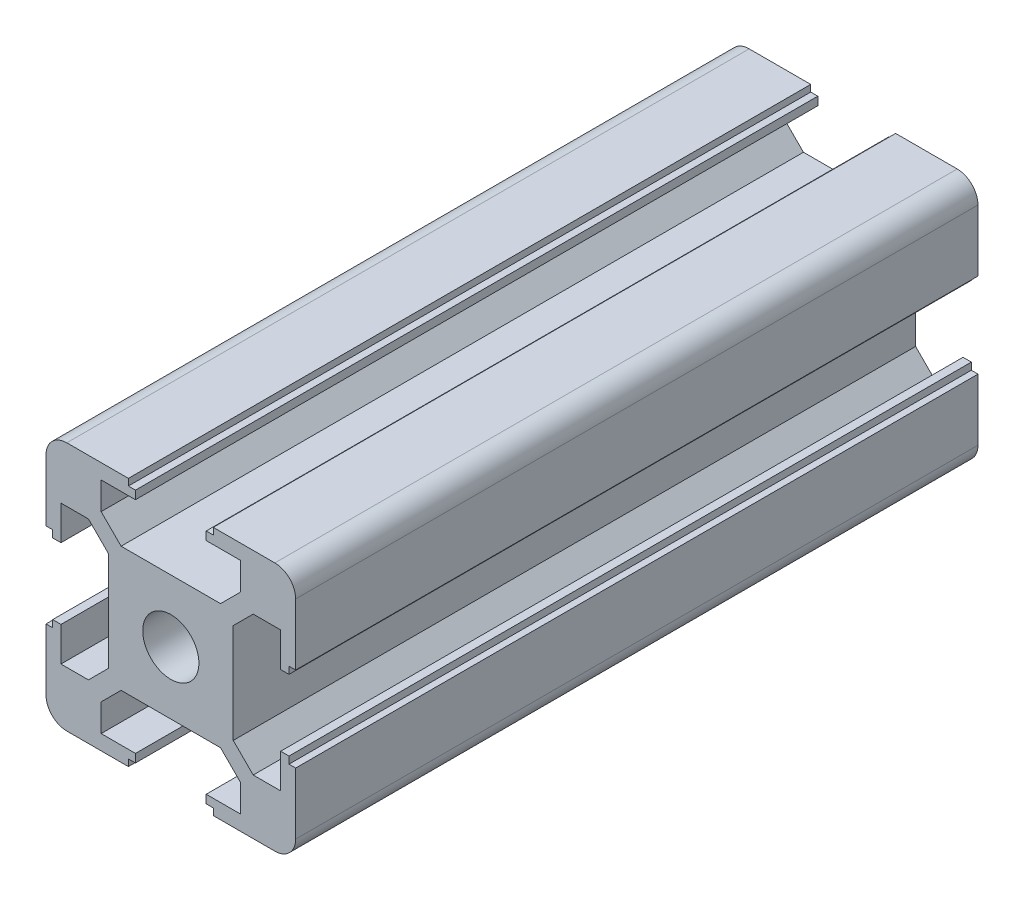
SolidWorks part; units mm, degrees
ref_plane "Front Plane" through (0, 0, 0) normal (0, 0, 1) x (1, 0, 0)
ref_plane "Top Plane" through (0, 0, 0) normal (0, 1, 0) x (1, 0, 0)
ref_plane "Right Plane" through (0, 0, 0) normal (1, 0, 0) x (0, 0, -1)
sketch "Sketch1" plane through (0, 0, 0) normal (0, 0, 1) x (1, 0, 0)
  line L1 (-15, -15) -> (15, -15)
  line L2 (-15, -15) -> (-15, 15)
  line L3 (-15, 15) -> (15, 15)
  line L4 (15, -15) -> (15, 15)
  line L5 (-15, -15) -> (15, 15) construction
  line L6 (-15, 15) -> (15, -15) construction
  point P0 (0, 0)
  dimension "D1" = 30
  dimension "D2" = 30
extrude "Boss-Extrude1" add sketch "Sketch1" along normal mid plane 82
sketch "Sketch2" plane through (0, 0, 41) normal (0, 0, 1) x (1, 0, 0)
  circle A0 centre (0, 0) radius 3.375
  dimension "D1" = 6.75
extrude "Cut-Extrude1" cut sketch "Sketch2" against normal through all
cosmetic thread "Cosmetic Thread1" parameters "D1"=12, "D2"=8
cosmetic thread "Cosmetic Thread2" parameters "D1"=12, "D2"=8
fillet "Fillet1" radius 2.5 4 edges at (15, -15, 0) (-15, -15, 0) (15, 15, 0) (-15, 15, 0)
sketch "Sketch3" plane through (0, 0, 41) normal (0, 0, 1) x (1, 0, 0)
  line L0 (0, -1000) -> (0, 49000) construction
  line L1 (0, 15) -> (-5.1, 15)
  line L2 (12.5, 15) -> (-12.5, 15) construction
  line L3 (-5.1, 15) -> (-5.1, 14.2)
  line L4 (-5.1, 14.2) -> (-4.25, 14.2)
  line L5 (-4.25, 14.2) -> (-4.25, 13.2)
  line L6 (-4.25, 13.2) -> (-8.375, 13.2)
  line L7 (-8.375, 13.2) -> (-8.375, 9.9)
  line L8 (-8.375, 9.9) -> (-5.975, 7.5)
  line L9 (-5.975, 7.5) -> (0, 7.5)
  line L10 (0, 7.5) -> (0, 15)
  dimension "D1" = 5.1
  dimension "D2" = 4.25
  dimension "D3" = 1.8
  dimension "D4" = 1
  dimension "D5" = 3.3
  dimension "D6" = 8.375
  dimension "D7" = 135
  dimension "D8" = 7.5
extrude "Cut-Extrude2" cut sketch "Sketch3" against normal through all
mirror "Mirror1" about plane through (0, 0, 0) normal (1, 0, 0) of "Cut-Extrude2"
pattern_circular "CirPattern1" count 4 over 360 about axis through (0, 0, 0) along (0, 0, 1) of "Mirror1", "Cut-Extrude2"
